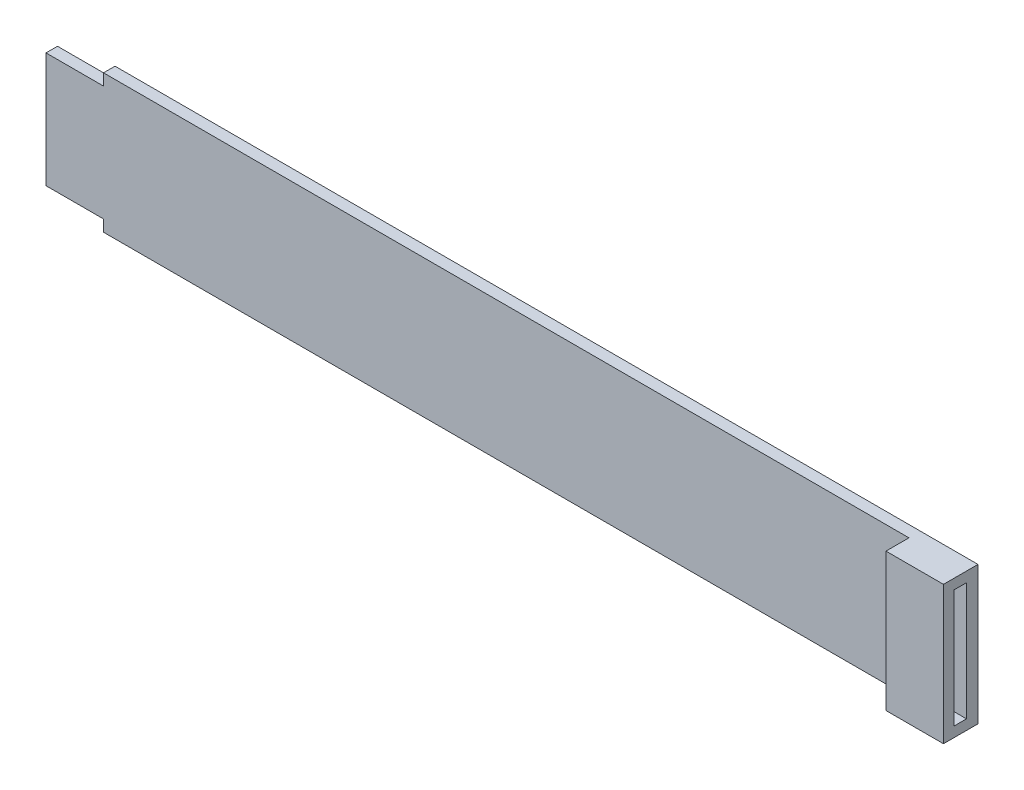
SolidWorks part; units mm, degrees
ref_plane "Alzado" through (0, 0, 0) normal (0, 0, 1) x (1, 0, 0)
ref_plane "Planta" through (0, 0, 0) normal (0, 1, 0) x (1, 0, 0)
ref_plane "Vista lateral" through (0, 0, 0) normal (1, 0, 0) x (0, 0, -1)
sketch "Croquis1" plane through (0, 0, 0) normal (0, 0, 1) x (1, 0, 0)
  line L0 (-8.5165, 1.2959) -> (1.4835, 1.2959)
  line L2 (-8.5165, 1.2959) -> (-8.5165, -18.7041)
  line L5 (1.4835, 1.2959) -> (1.4835, 3.2959)
  line L6 (1.4835, 3.2959) -> (151.4835, 3.2959)
  line L7 (151.4835, 3.2959) -> (151.4835, -20.7041)
  line L8 (151.4835, -20.7041) -> (1.4835, -20.7041)
  line L9 (1.4835, -20.7041) -> (1.4835, -18.7041)
  line L10 (1.4835, -18.7041) -> (-8.5165, -18.7041)
  dimension "D2" = 20
extrude "Saliente-Extruir1" add sketch "Croquis1" along normal blind 2
sketch "Croquis3" plane through (151.4835, 0, 0) normal (1, 0, 0) x (0, 0, -1)
  line L0 (-2, 3.2959) -> (-6, 3.2959)
  line L1 (-6, 3.2959) -> (-6, -20.7041)
  line L2 (-6, -20.7041) -> (-2, -20.7041)
  line L3 (-2, -20.7041) -> (-2, 3.2959)
  line L5 (-4.2, 1.5459) -> (-2, 1.5459)
  line L6 (-4.2, 1.5459) -> (-4.2, -18.9541)
  line L7 (-4.2, -18.9541) -> (-2, -18.9541)
  line L8 (-2, 1.5459) -> (-2, -18.9541)
  line M7 (-2, 3.2959) -> (-2, -20.7041)
  dimension "D1" = 1.8
  dimension "D2" = 2.2
  dimension "D3" = 1.75
  dimension "D4" = 20.5
extrude "Saliente-Extruir2" add sketch "Croquis3" against normal blind 10 contours L7 L6 L5 L0 L1 L2 M7
